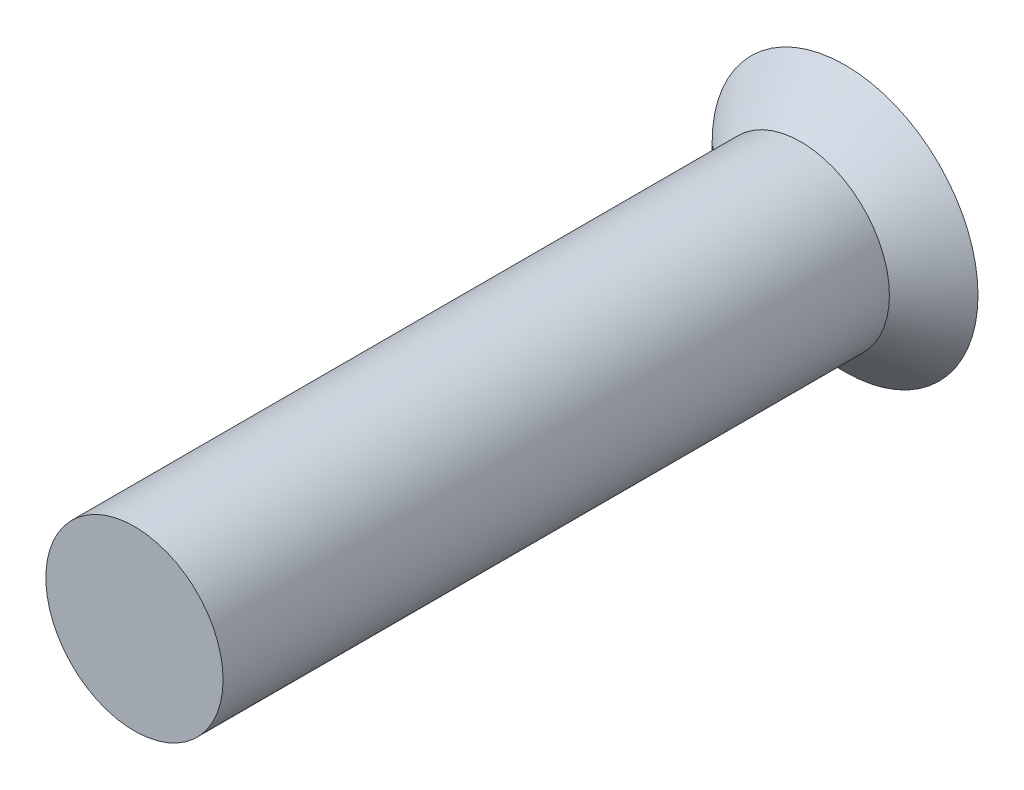
SolidWorks part; units mm, degrees
material "AISI 1020 Steel, Cold Rolled"
ref_plane "Front Plane" through (0, 0, 0) normal (0, 0, 1) x (1, 0, 0)
ref_plane "Top Plane" through (0, 0, 0) normal (0, 1, 0) x (1, 0, 0)
ref_plane "Right Plane" through (0, 0, 0) normal (1, 0, 0) x (0, 0, -1)
sketch "Sketch1" plane through (0, 0, 0) normal (0, 0, 1) x (1, 0, 0)
  circle A0 centre (0, 0) radius 0.5
  dimension "D1" = 1
extrude "Boss-Extrude1" add sketch "Sketch1" along normal mid plane 3.76 contours A0
sketch "Sketch2" plane through (0, 0, 0) normal (1, 0, 0) x (0, 0, -1)
  line L0 (1.88, 0.5) -> (2.13, 0.75)
  line L1 (2.13, 0.75) -> (2.13, 0)
  line L2 (2.13, 0) -> (1.88, 0)
  line L3 (1.88, -0.5) -> (1.88, 0.5) construction
  line L4 (1.88, 0) -> (1.88, 0.5)
  dimension "D1" = 0.25
ref_axis "Axis1" through (0, 0, 2.0805) along (0, 0, -1)
revolve "Revolve1" add sketch "Sketch2" angle 360 about axis through (0, 0, 2.0805) along (0, 0, -1)
sketch "Sketch3" plane through (0, 0, -2.13) normal (0, 0, -1) x (-1, 0, 0)
  line L0 (-0.1, 0.6) -> (-0.1, 0.1)
  line L1 (-0.1, 0.1) -> (-0.6, 0.1)
  line L2 (-0.6, 0.1) -> (-0.6, -0.1)
  line L3 (-0.6, -0.1) -> (-0.1, -0.1)
  line L4 (-0.1, -0.1) -> (-0.1, -0.6)
  line L5 (-0.1, -0.6) -> (0.1, -0.6)
  line L6 (0.1, -0.6) -> (0.1, -0.1)
  line L7 (0.1, -0.1) -> (0.6, -0.1)
  line L8 (0.6, -0.1) -> (0.6, 0.1)
  line L9 (0.6, 0.1) -> (0.1, 0.1)
  line L10 (0.1, 0.1) -> (0.1, 0.6)
  line L11 (0.1, 0.6) -> (-0.1, 0.6)
  line L12 (0.825, 0) -> (-0.825, 0) construction
  line L13 (0, 0.825) -> (0, -0.825) construction
  point P12 (-0.6, 0)
  point P17 (0, 0.6)
  dimension "D1" = 0.2
  dimension "D2" = 0.2
  dimension "D3" = 0.2
  dimension "D4" = 0.5
  dimension "D5" = 0.5
extrude "Cut-Extrude1" cut sketch "Sketch3" against normal blind 0.1
